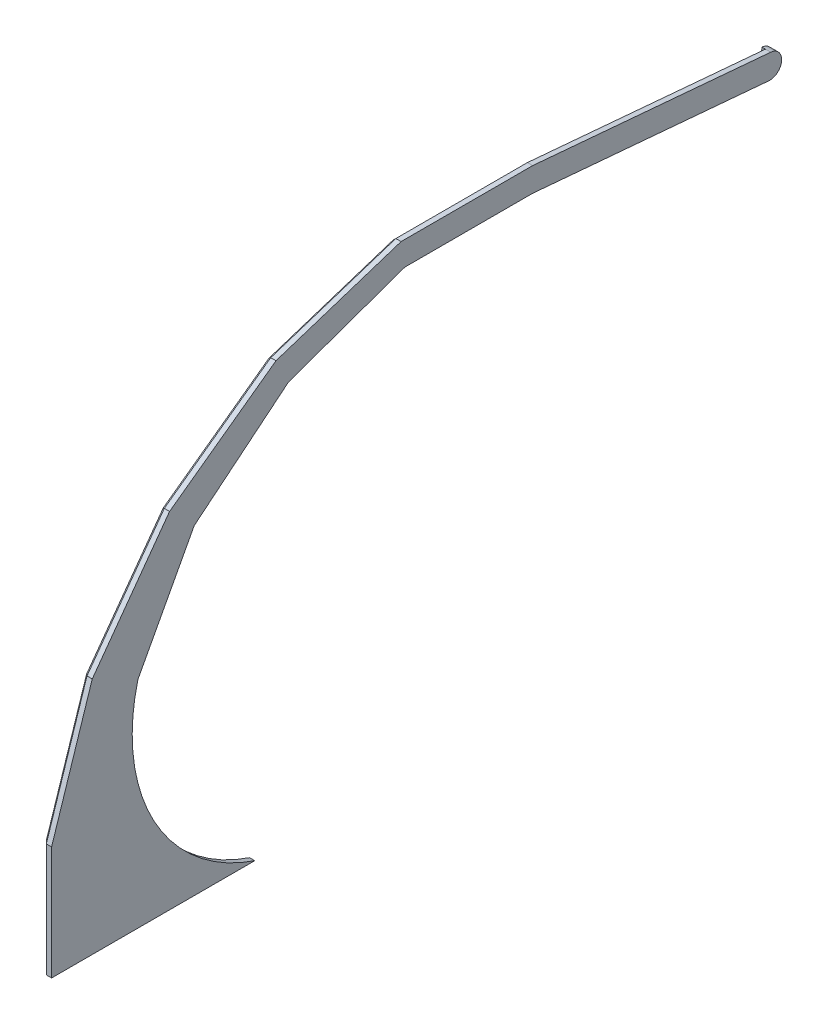
SolidWorks part; units mm, degrees
ref_plane "Front Plane" through (0, 0, 0) normal (0, 0, 1) x (1, 0, 0)
ref_plane "Top Plane" through (0, 0, 0) normal (0, 1, 0) x (1, 0, 0)
ref_plane "Right Plane" through (0, 0, 0) normal (1, 0, 0) x (0, 0, -1)
sketch "Sketch1" plane through (0, 0, 0) normal (1, 0, 0) x (0, 0, -1)
  line L0 (12.6153, -92.6333) -> (182.6153, -92.6333)
  line L6 (415.1195, 274.7215) -> (612.6153, 257.4428)
  line L8 (614.3584, 277.3667) -> (415.1195, 294.7979)
  line L9 (12.6153, -92.6333) -> (12.6153, 2.3615)
  line L10 (12.6153, 2.3615) -> (46.6281, 107.0421)
  line L11 (46.6281, 107.0421) -> (111.3243, 196.0888)
  line L12 (111.3243, 196.0888) -> (200.371, 260.7851)
  line L13 (200.371, 260.7851) -> (305.0517, 294.7979)
  line L14 (305.0517, 294.7979) -> (415.1195, 294.7979)
  line L15 (452.6153, 271.441) -> (183.2145, -92.6333) construction
  line L16 (452.6153, 271.441) -> (634.136, -92.6333) construction
  line L20 (84.8259, 87.5794) -> (131.9298, 175.4834)
  line L21 (131.9298, 175.4834) -> (210.8849, 240.1505)
  line L22 (210.8849, 240.1505) -> (308.2365, 274.69)
  line L23 (308.2365, 274.69) -> (415.1195, 274.7215)
  line L24 (111.3243, 196.0888) -> (131.9298, 175.4834) construction
  line L25 (200.371, 260.7851) -> (210.8849, 240.1505) construction
  line L26 (46.6281, 107.0421) -> (84.8259, 87.5794) construction
  line L27 (183.2145, -92.6333) -> (634.136, -92.6333) construction
  line L28 (305.0517, 294.7979) -> (308.2365, 274.69) construction
  arc A0 (84.8259, 87.5794) -> (182.6153, -92.6333) centre (230.5143, 49.9965) ccw
  arc A2 (612.6153, 257.4428) -> (614.3584, 277.3667) centre (613.4869, 267.4048) ccw
  dimension "D1" = 600
  dimension "D2" = 200
  dimension "D3" = 5
  dimension "D4" = 370
  dimension "D5" = 20
  dimension "D12" = 162
  dimension "D13" = 162
  dimension "D14" = 162
  dimension "D15" = 162
  dimension "D16" = 170
  dimension "D18" = 63
  dimension "D19" = 58.5
  dimension "D20" = 160
  dimension "D6" = 81
  dimension "D7" = 81
  dimension "D8" = 81
  dimension "D17" = 162
  dimension "D21" = 81
extrude "Boss-Extrude1" add sketch "Sketch1" against normal blind 4.4
sketch "Sketch2" plane through (-4.4, 0, 0) normal (-1, 0, 0) x (0, 0, 1)
  line L0 (-614.3584, 277.3667) -> (-614.0969, 274.3781)
  line L1 (-614.0969, 274.3781) -> (-415.1195, 291.7864)
  line L2 (-612.8768, 260.4314) -> (-415.25, 277.7215)
  line L3 (-612.8768, 260.4314) -> (-612.6153, 257.4428)
  line L4 (-415.1195, 294.7979) -> (-415.1195, 274.7215) construction
  line L5 (-305.0517, 294.7979) -> (-308.2365, 274.69) construction
  line L6 (-200.371, 260.7851) -> (-210.8849, 240.1505) construction
  line L7 (-415.1195, 291.7864) -> (-305.5287, 291.7864)
  line L8 (-415.25, 277.7215) -> (-307.7613, 277.6898)
  line L9 (-307.7613, 277.6898) -> (-209.5176, 242.8338)
  line L10 (-305.5287, 291.7864) -> (-201.7552, 258.0684)
  line L11 (-111.3243, 196.0888) -> (-131.9298, 175.4834) construction
  line L12 (-46.6281, 107.0421) -> (-84.8259, 87.5794) construction
  line L13 (-12.6153, 2.3615) -> (4.7357, 1.8595) construction
  line L14 (-201.7552, 258.0684) -> (-113.4803, 193.9329)
  line L15 (-113.4803, 193.9329) -> (-49.3448, 105.6579)
  line L16 (-49.3448, 105.6579) -> (-15.8118, 2.4539)
  line L17 (-15.8118, 2.4539) -> (-15.8118, -92.6333)
  line L18 (-12.6153, -92.6333) -> (-182.6153, -92.6333) construction
  line L19 (-15.8118, -92.6333) -> (-101.9058, -92.6333)
  line L20 (-101.9058, -92.6333) -> (-66.1481, 3.9103)
  line L21 (-66.1481, 3.9103) -> (-82.1529, 88.9413)
  line L22 (-82.1529, 88.9413) -> (-129.839, 177.5741)
  line L23 (-129.839, 177.5741) -> (-209.5176, 242.8338)
  line L25 (-45.9153, -59.0333) -> (-35.3153, -59.0333)
  line L26 (-415.1195, 294.7979) -> (-305.0517, 294.7979) construction
  line L27 (-308.2365, 274.69) -> (-415.1195, 274.7215) construction
  line L28 (-614.3584, 277.3667) -> (-415.1195, 294.7979) construction
  line L29 (-415.1195, 274.7215) -> (-612.6153, 257.4428) construction
  line L30 (-305.0517, 294.7979) -> (-200.371, 260.7851) construction
  line L31 (-210.8849, 240.1505) -> (-308.2365, 274.69) construction
  line L32 (-200.371, 260.7851) -> (-111.3243, 196.0888) construction
  line L33 (-131.9298, 175.4834) -> (-210.8849, 240.1505) construction
  line L34 (-111.3243, 196.0888) -> (-46.6281, 107.0421) construction
  line L35 (-45.9153, -59.0333) -> (-45.9153, -62.6333)
  line L36 (-46.6281, 107.0421) -> (-12.6153, 2.3615) construction
  line L37 (-12.6153, 2.3615) -> (-12.6153, -92.6333) construction
  line L38 (-45.9153, -62.6333) -> (-35.3153, -62.6333)
  line L39 (-563.8078, 273.2568) -> (-553.2482, 274.1807)
  line L40 (-563.8078, 273.2568) -> (-563.4941, 269.6705)
  line L41 (-563.4941, 269.6705) -> (-552.9344, 270.5944)
  line L42 (-553.2482, 274.1807) -> (-552.9344, 270.5944)
  line L43 (-473.5526, 281.1532) -> (-462.9929, 282.077)
  line L44 (-473.5526, 281.1532) -> (-473.2388, 277.5669)
  line L45 (-473.2388, 277.5669) -> (-462.6792, 278.4907)
  line L46 (-462.9929, 282.077) -> (-462.6792, 278.4907)
  line L47 (-618.9236, 268.736) -> (-608.3639, 269.6598)
  line L48 (-618.9236, 268.736) -> (-618.6098, 265.1497)
  line L49 (-618.6098, 265.1497) -> (-608.0501, 266.0735)
  line L50 (-608.3639, 269.6598) -> (-608.0501, 266.0735)
  line L51 (-35.3153, -59.0333) -> (-35.3153, -62.6333)
  line L52 (-62.7038, -4.0653) -> (-59.3279, -5.3157)
  line L53 (-62.7038, -4.0653) -> (-66.3854, -14.0054)
  line L54 (-66.3854, -14.0054) -> (-63.0095, -15.2558)
  line L55 (-59.3279, -5.3157) -> (-63.0095, -15.2558)
  arc A0 (-614.3584, 277.3667) -> (-612.6153, 257.4428) centre (-613.4869, 267.4048) ccw
  point P89 (-40.6153, -62.6333)
  point P90 (-56.6262, -17.6333)
  point P91 (0, 0)
  point P92 (0, 0)
  point P93 (0, 0)
  point P94 (-52.1955, -7.6705)
  point P95 (-55.8153, -17.6333)
  point P96 (-55.8153, -17.6333)
  point P97 (-58.7655, -17.6333)
  point P98 (-55.9709, -17.6333)
  point P99 (-59.7082, -17.6333)
  point P100 (-59.4164, -17.6333)
  point P101 (-55.4903, -18.7101)
  dimension "D1" = 3
  dimension "D2" = 3
  dimension "D3" = 3.6
  dimension "D4" = 10.6
  dimension "D5" = 50
  dimension "D6" = 3.6
  dimension "D7" = 10.6
  dimension "D8" = 80
  dimension "D9" = 8.5
  dimension "D10" = 8.5
  dimension "D11" = 10.6
  dimension "D12" = 5.3
  dimension "D13" = 3.6
  dimension "D14" = 1.8
  dimension "D15" = 3
  dimension "D16" = 3
  dimension "D17" = 10.6
  dimension "D18" = 3.6
  dimension "D21" = 30
  dimension "D22" = 28
  dimension "D19" = 3.6
  dimension "D20" = 10.6
  dimension "D23" = 6
extrude "Boss-Extrude2" add sketch "Sketch2" along normal blind 3
equation "\"Phone height\"= 370"
equation "\"edge distance from wall\"= 600"
equation "\"phone angle\"= 5"
equation "\"D1@Sketch1\"=\"edge distance from wall\""
equation "\"base depth\"= 170"
equation "\"width\"= 108"
equation "\"Phone segment length\"= 200"
equation "\"D2@Sketch1\"=\"Phone segment length\""
equation "\"D3@Sketch1\"=\"phone angle\""
equation "\"D4@Sketch1\"=\"Phone height\""
equation "\"Phone segment thick\"= 20"
equation "\"D5@Sketch1\"=\"Phone segment thick\""
equation "\"Phone segment acute angle\"= 1"
equation "\"D16@Sketch1\"=\"base depth\""
equation "\"upper segment count\"= 6"
equation "\"lower segment count\"= 5"
equation "\"upper segment angle\"= 180 - ( 90 / ( \"upper segment count\" - 1 ) )"
equation "\"D12@Sketch1\"=\"upper segment angle\""
equation "\"D13@Sketch1\"=\"upper segment angle\""
equation "\"D14@Sketch1\"=\"upper segment angle\""
equation "\"D15@Sketch1\"=\"upper segment angle\""
equation "\"lower segment angle\"= 180 - ( 90 / ( \"lower segment count\" - 1 ) )"
equation "\"fov\"=63"
equation "\"D18@Sketch1\"=\"fov\""
equation "\"D19@Sketch1\"=(180-\"fov\")/2"
equation "\"D6@Sketch1\"=\"upper segment angle\"/2"
equation "\"D7@Sketch1\"=\"upper segment angle\"/2"
equation "\"D8@Sketch1\"=\"upper segment angle\"/2"
equation "\"D17@Sketch1\"=\"upper segment angle\""
equation "\"D21@Sketch1\"=\"upper segment angle\"/2"
equation "\"Thicker acrylic\"= 4.4"
equation "\"Thinner acrylic\"= 3"
equation "\"D1@Boss-Extrude1\"=\"Thicker acrylic\""
equation "\"D1@Sketch2\"=\"Thinner acrylic\""
equation "\"D2@Sketch2\"=\"Thinner acrylic\""
equation "\"phone thick\"= 8.5"
equation "\"phone support width\"= 10"
equation "\"fit\"= 0.6"
equation "\"D3@Sketch2\"=\"Thinner acrylic\"+\"fit\""
equation "\"D4@Sketch2\"=\"phone support width\"+\"fit\""
equation "\"D5@Sketch2\"=50"
equation "\"D6@Sketch2\"=\"Thinner acrylic\"+\"fit\""
equation "\"D7@Sketch2\"=\"phone support width\"+\"fit\""
equation "\"D9@Sketch2\"=\"phone thick\""
equation "\"D10@Sketch2\"=\"phone thick\""
equation "\"D1@Boss-Extrude2\"=\"Thinner acrylic\""
equation "\"D11@Sketch2\"=\"phone support width\"+\"fit\""
equation "\"D12@Sketch2\"=\"D11@Sketch2\"/2"
equation "\"D13@Sketch2\"=\"Thinner acrylic\"+\"fit\""
equation "\"D14@Sketch2\"=\"D13@Sketch2\"/2"
equation "\"phone support length\"= 98.5"
equation "\"D15@Sketch2\"=\"Thinner acrylic\""
equation "\"D16@Sketch2\"=\"Thinner acrylic\""
equation "\"D17@Sketch2\"=\"phone support width\"+\"fit\""
equation "\"D18@Sketch2\"=\"Thinner acrylic\"+\"fit\""
equation "\"D19@Sketch2\"=\"Thinner acrylic\"+\"fit\""
equation "\"D20@Sketch2\"=\"phone support width\"+\"fit\""
